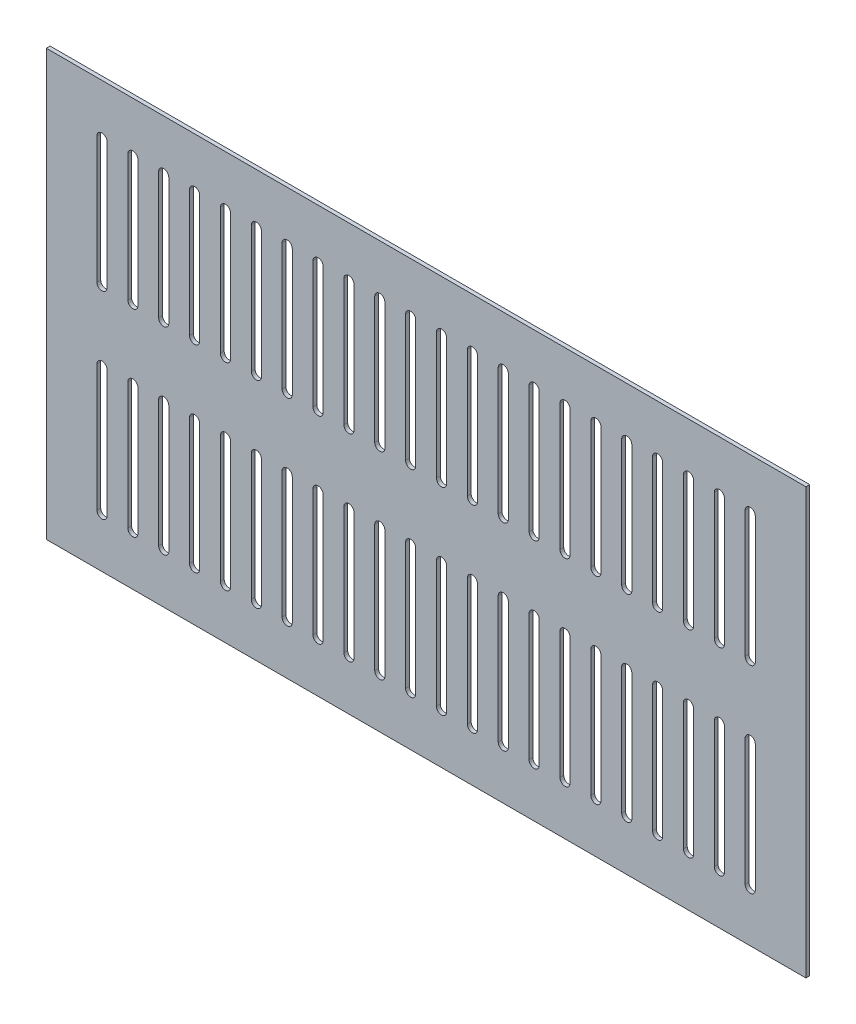
SolidWorks part; units mm, degrees
ref_plane "Ön Düzlem" through (0, 0, 0) normal (0, 0, 1) x (1, 0, 0)
ref_plane "Üst Düzlem" through (0, 0, 0) normal (0, 1, 0) x (1, 0, 0)
ref_plane "Sağ Düzlem" through (0, 0, 0) normal (1, 0, 0) x (0, 0, -1)
sketch "Çizim1" plane through (0, 0, 0) normal (0, 0, 1) x (1, 0, 0)
  line L0 (44, -40) -> (44, -140) construction
  line L1 (0, 0) -> (600, 0)
  line L2 (0, 0) -> (0, -336)
  line L3 (0, -336) -> (600, -336)
  line L4 (600, 0) -> (600, -336)
  line L5 (48, -40) -> (48, -140)
  line L6 (40, -40) -> (40, -140)
  line L7 (64.381, -40) -> (64.381, -140)
  line L8 (72.381, -40) -> (72.381, -140)
  line L9 (68.381, -40) -> (68.381, -140) construction
  line L10 (88.7619, -40) -> (88.7619, -140)
  line L11 (96.7619, -40) -> (96.7619, -140)
  line L12 (92.7619, -40) -> (92.7619, -140) construction
  line L13 (113.1429, -40) -> (113.1429, -140)
  line L14 (121.1429, -40) -> (121.1429, -140)
  line L15 (117.1429, -40) -> (117.1429, -140) construction
  line L16 (137.5238, -40) -> (137.5238, -140)
  line L17 (145.5238, -40) -> (145.5238, -140)
  line L18 (141.5238, -40) -> (141.5238, -140) construction
  line L19 (161.9048, -40) -> (161.9048, -140)
  line L20 (169.9048, -40) -> (169.9048, -140)
  line L21 (165.9048, -40) -> (165.9048, -140) construction
  line L22 (186.2857, -40) -> (186.2857, -140)
  line L23 (194.2857, -40) -> (194.2857, -140)
  line L24 (190.2857, -40) -> (190.2857, -140) construction
  line L25 (210.6667, -40) -> (210.6667, -140)
  line L26 (218.6667, -40) -> (218.6667, -140)
  line L27 (214.6667, -40) -> (214.6667, -140) construction
  line L28 (235.0476, -40) -> (235.0476, -140)
  line L29 (243.0476, -40) -> (243.0476, -140)
  line L30 (239.0476, -40) -> (239.0476, -140) construction
  line L31 (259.4286, -40) -> (259.4286, -140)
  line L32 (267.4286, -40) -> (267.4286, -140)
  line L33 (263.4286, -40) -> (263.4286, -140) construction
  line L34 (283.8095, -40) -> (283.8095, -140)
  line L35 (291.8095, -40) -> (291.8095, -140)
  line L36 (287.8095, -40) -> (287.8095, -140) construction
  line L37 (308.1905, -40) -> (308.1905, -140)
  line L38 (316.1905, -40) -> (316.1905, -140)
  line L39 (312.1905, -40) -> (312.1905, -140) construction
  line L40 (332.5714, -40) -> (332.5714, -140)
  line L41 (340.5714, -40) -> (340.5714, -140)
  line L42 (336.5714, -40) -> (336.5714, -140) construction
  line L43 (356.9524, -40) -> (356.9524, -140)
  line L44 (364.9524, -40) -> (364.9524, -140)
  line L45 (360.9524, -40) -> (360.9524, -140) construction
  line L46 (381.3333, -40) -> (381.3333, -140)
  line L47 (389.3333, -40) -> (389.3333, -140)
  line L48 (385.3333, -40) -> (385.3333, -140) construction
  line L49 (405.7143, -40) -> (405.7143, -140)
  line L50 (413.7143, -40) -> (413.7143, -140)
  line L51 (409.7143, -40) -> (409.7143, -140) construction
  line L52 (430.0952, -40) -> (430.0952, -140)
  line L53 (438.0952, -40) -> (438.0952, -140)
  line L54 (434.0952, -40) -> (434.0952, -140) construction
  line L55 (454.4762, -40) -> (454.4762, -140)
  line L56 (462.4762, -40) -> (462.4762, -140)
  line L57 (458.4762, -40) -> (458.4762, -140) construction
  line L58 (478.8571, -40) -> (478.8571, -140)
  line L59 (486.8571, -40) -> (486.8571, -140)
  line L60 (482.8571, -40) -> (482.8571, -140) construction
  line L61 (503.2381, -40) -> (503.2381, -140)
  line L62 (511.2381, -40) -> (511.2381, -140)
  line L63 (507.2381, -40) -> (507.2381, -140) construction
  line L64 (527.619, -40) -> (527.619, -140)
  line L65 (535.619, -40) -> (535.619, -140)
  line L66 (531.619, -40) -> (531.619, -140) construction
  line L67 (552, -40) -> (552, -140)
  line L68 (560, -40) -> (560, -140)
  line L69 (556, -40) -> (556, -140) construction
  line L70 (64.381, -196) -> (64.381, -296)
  line L71 (72.381, -196) -> (72.381, -296)
  line L72 (68.381, -196) -> (68.381, -296) construction
  line L73 (88.7619, -196) -> (88.7619, -296)
  line L74 (96.7619, -196) -> (96.7619, -296)
  line L75 (92.7619, -196) -> (92.7619, -296) construction
  line L76 (113.1429, -196) -> (113.1429, -296)
  line L77 (121.1429, -196) -> (121.1429, -296)
  line L78 (117.1429, -196) -> (117.1429, -296) construction
  line L79 (137.5238, -196) -> (137.5238, -296)
  line L80 (145.5238, -196) -> (145.5238, -296)
  line L81 (141.5238, -196) -> (141.5238, -296) construction
  line L82 (161.9048, -196) -> (161.9048, -296)
  line L83 (169.9048, -196) -> (169.9048, -296)
  line L84 (165.9048, -196) -> (165.9048, -296) construction
  line L85 (186.2857, -196) -> (186.2857, -296)
  line L86 (194.2857, -196) -> (194.2857, -296)
  line L87 (190.2857, -196) -> (190.2857, -296) construction
  line L88 (210.6667, -196) -> (210.6667, -296)
  line L89 (218.6667, -196) -> (218.6667, -296)
  line L90 (214.6667, -196) -> (214.6667, -296) construction
  line L91 (235.0476, -196) -> (235.0476, -296)
  line L92 (243.0476, -196) -> (243.0476, -296)
  line L93 (239.0476, -196) -> (239.0476, -296) construction
  line L94 (259.4286, -196) -> (259.4286, -296)
  line L95 (267.4286, -196) -> (267.4286, -296)
  line L96 (263.4286, -196) -> (263.4286, -296) construction
  line L97 (283.8095, -196) -> (283.8095, -296)
  line L98 (291.8095, -196) -> (291.8095, -296)
  line L99 (287.8095, -196) -> (287.8095, -296) construction
  line L100 (308.1905, -196) -> (308.1905, -296)
  line L101 (316.1905, -196) -> (316.1905, -296)
  line L102 (312.1905, -196) -> (312.1905, -296) construction
  line L103 (332.5714, -196) -> (332.5714, -296)
  line L104 (340.5714, -196) -> (340.5714, -296)
  line L105 (336.5714, -196) -> (336.5714, -296) construction
  line L106 (356.9524, -196) -> (356.9524, -296)
  line L107 (364.9524, -196) -> (364.9524, -296)
  line L108 (360.9524, -196) -> (360.9524, -296) construction
  line L109 (381.3333, -196) -> (381.3333, -296)
  line L110 (389.3333, -196) -> (389.3333, -296)
  line L111 (385.3333, -196) -> (385.3333, -296) construction
  line L112 (405.7143, -196) -> (405.7143, -296)
  line L113 (413.7143, -196) -> (413.7143, -296)
  line L114 (409.7143, -196) -> (409.7143, -296) construction
  line L115 (430.0952, -196) -> (430.0952, -296)
  line L116 (438.0952, -196) -> (438.0952, -296)
  line L117 (434.0952, -196) -> (434.0952, -296) construction
  line L118 (454.4762, -196) -> (454.4762, -296)
  line L119 (462.4762, -196) -> (462.4762, -296)
  line L120 (458.4762, -196) -> (458.4762, -296) construction
  line L121 (478.8571, -196) -> (478.8571, -296)
  line L122 (486.8571, -196) -> (486.8571, -296)
  line L123 (482.8571, -196) -> (482.8571, -296) construction
  line L124 (503.2381, -196) -> (503.2381, -296)
  line L125 (511.2381, -196) -> (511.2381, -296)
  line L126 (507.2381, -196) -> (507.2381, -296) construction
  line L127 (527.619, -196) -> (527.619, -296)
  line L128 (535.619, -196) -> (535.619, -296)
  line L129 (531.619, -196) -> (531.619, -296) construction
  line L130 (552, -196) -> (552, -296)
  line L131 (560, -196) -> (560, -296)
  line L132 (556, -196) -> (556, -296) construction
  line L133 (40, -196) -> (40, -296)
  line L134 (48, -196) -> (48, -296)
  line L135 (44, -196) -> (44, -296) construction
  arc A0 (48, -40) -> (40, -40) centre (44, -40) ccw
  arc A1 (40, -140) -> (48, -140) centre (44, -140) ccw
  arc A2 (72.381, -40) -> (64.381, -40) centre (68.381, -40) ccw
  arc A3 (64.381, -140) -> (72.381, -140) centre (68.381, -140) ccw
  arc A4 (96.7619, -40) -> (88.7619, -40) centre (92.7619, -40) ccw
  arc A5 (88.7619, -140) -> (96.7619, -140) centre (92.7619, -140) ccw
  arc A6 (121.1429, -40) -> (113.1429, -40) centre (117.1429, -40) ccw
  arc A7 (113.1429, -140) -> (121.1429, -140) centre (117.1429, -140) ccw
  arc A8 (145.5238, -40) -> (137.5238, -40) centre (141.5238, -40) ccw
  arc A9 (137.5238, -140) -> (145.5238, -140) centre (141.5238, -140) ccw
  arc A10 (169.9048, -40) -> (161.9048, -40) centre (165.9048, -40) ccw
  arc A11 (161.9048, -140) -> (169.9048, -140) centre (165.9048, -140) ccw
  arc A12 (194.2857, -40) -> (186.2857, -40) centre (190.2857, -40) ccw
  arc A13 (186.2857, -140) -> (194.2857, -140) centre (190.2857, -140) ccw
  arc A14 (218.6667, -40) -> (210.6667, -40) centre (214.6667, -40) ccw
  arc A15 (210.6667, -140) -> (218.6667, -140) centre (214.6667, -140) ccw
  arc A16 (243.0476, -40) -> (235.0476, -40) centre (239.0476, -40) ccw
  arc A17 (235.0476, -140) -> (243.0476, -140) centre (239.0476, -140) ccw
  arc A18 (267.4286, -40) -> (259.4286, -40) centre (263.4286, -40) ccw
  arc A19 (259.4286, -140) -> (267.4286, -140) centre (263.4286, -140) ccw
  arc A20 (291.8095, -40) -> (283.8095, -40) centre (287.8095, -40) ccw
  arc A21 (283.8095, -140) -> (291.8095, -140) centre (287.8095, -140) ccw
  arc A22 (316.1905, -40) -> (308.1905, -40) centre (312.1905, -40) ccw
  arc A23 (308.1905, -140) -> (316.1905, -140) centre (312.1905, -140) ccw
  arc A24 (340.5714, -40) -> (332.5714, -40) centre (336.5714, -40) ccw
  arc A25 (332.5714, -140) -> (340.5714, -140) centre (336.5714, -140) ccw
  arc A26 (364.9524, -40) -> (356.9524, -40) centre (360.9524, -40) ccw
  arc A27 (356.9524, -140) -> (364.9524, -140) centre (360.9524, -140) ccw
  arc A28 (389.3333, -40) -> (381.3333, -40) centre (385.3333, -40) ccw
  arc A29 (381.3333, -140) -> (389.3333, -140) centre (385.3333, -140) ccw
  arc A30 (413.7143, -40) -> (405.7143, -40) centre (409.7143, -40) ccw
  arc A31 (405.7143, -140) -> (413.7143, -140) centre (409.7143, -140) ccw
  arc A32 (438.0952, -40) -> (430.0952, -40) centre (434.0952, -40) ccw
  arc A33 (430.0952, -140) -> (438.0952, -140) centre (434.0952, -140) ccw
  arc A34 (462.4762, -40) -> (454.4762, -40) centre (458.4762, -40) ccw
  arc A35 (454.4762, -140) -> (462.4762, -140) centre (458.4762, -140) ccw
  arc A36 (486.8571, -40) -> (478.8571, -40) centre (482.8571, -40) ccw
  arc A37 (478.8571, -140) -> (486.8571, -140) centre (482.8571, -140) ccw
  arc A38 (511.2381, -40) -> (503.2381, -40) centre (507.2381, -40) ccw
  arc A39 (503.2381, -140) -> (511.2381, -140) centre (507.2381, -140) ccw
  arc A40 (535.619, -40) -> (527.619, -40) centre (531.619, -40) ccw
  arc A41 (527.619, -140) -> (535.619, -140) centre (531.619, -140) ccw
  arc A42 (560, -40) -> (552, -40) centre (556, -40) ccw
  arc A43 (552, -140) -> (560, -140) centre (556, -140) ccw
  arc A44 (72.381, -196) -> (64.381, -196) centre (68.381, -196) ccw
  arc A45 (64.381, -296) -> (72.381, -296) centre (68.381, -296) ccw
  arc A46 (96.7619, -196) -> (88.7619, -196) centre (92.7619, -196) ccw
  arc A47 (88.7619, -296) -> (96.7619, -296) centre (92.7619, -296) ccw
  arc A48 (121.1429, -196) -> (113.1429, -196) centre (117.1429, -196) ccw
  arc A49 (113.1429, -296) -> (121.1429, -296) centre (117.1429, -296) ccw
  arc A50 (145.5238, -196) -> (137.5238, -196) centre (141.5238, -196) ccw
  arc A51 (137.5238, -296) -> (145.5238, -296) centre (141.5238, -296) ccw
  arc A52 (169.9048, -196) -> (161.9048, -196) centre (165.9048, -196) ccw
  arc A53 (161.9048, -296) -> (169.9048, -296) centre (165.9048, -296) ccw
  arc A54 (194.2857, -196) -> (186.2857, -196) centre (190.2857, -196) ccw
  arc A55 (186.2857, -296) -> (194.2857, -296) centre (190.2857, -296) ccw
  arc A56 (218.6667, -196) -> (210.6667, -196) centre (214.6667, -196) ccw
  arc A57 (210.6667, -296) -> (218.6667, -296) centre (214.6667, -296) ccw
  arc A58 (243.0476, -196) -> (235.0476, -196) centre (239.0476, -196) ccw
  arc A59 (235.0476, -296) -> (243.0476, -296) centre (239.0476, -296) ccw
  arc A60 (267.4286, -196) -> (259.4286, -196) centre (263.4286, -196) ccw
  arc A61 (259.4286, -296) -> (267.4286, -296) centre (263.4286, -296) ccw
  arc A62 (291.8095, -196) -> (283.8095, -196) centre (287.8095, -196) ccw
  arc A63 (283.8095, -296) -> (291.8095, -296) centre (287.8095, -296) ccw
  arc A64 (316.1905, -196) -> (308.1905, -196) centre (312.1905, -196) ccw
  arc A65 (308.1905, -296) -> (316.1905, -296) centre (312.1905, -296) ccw
  arc A66 (340.5714, -196) -> (332.5714, -196) centre (336.5714, -196) ccw
  arc A67 (332.5714, -296) -> (340.5714, -296) centre (336.5714, -296) ccw
  arc A68 (364.9524, -196) -> (356.9524, -196) centre (360.9524, -196) ccw
  arc A69 (356.9524, -296) -> (364.9524, -296) centre (360.9524, -296) ccw
  arc A70 (389.3333, -196) -> (381.3333, -196) centre (385.3333, -196) ccw
  arc A71 (381.3333, -296) -> (389.3333, -296) centre (385.3333, -296) ccw
  arc A72 (413.7143, -196) -> (405.7143, -196) centre (409.7143, -196) ccw
  arc A73 (405.7143, -296) -> (413.7143, -296) centre (409.7143, -296) ccw
  arc A74 (438.0952, -196) -> (430.0952, -196) centre (434.0952, -196) ccw
  arc A75 (430.0952, -296) -> (438.0952, -296) centre (434.0952, -296) ccw
  arc A76 (462.4762, -196) -> (454.4762, -196) centre (458.4762, -196) ccw
  arc A77 (454.4762, -296) -> (462.4762, -296) centre (458.4762, -296) ccw
  arc A78 (486.8571, -196) -> (478.8571, -196) centre (482.8571, -196) ccw
  arc A79 (478.8571, -296) -> (486.8571, -296) centre (482.8571, -296) ccw
  arc A80 (511.2381, -196) -> (503.2381, -196) centre (507.2381, -196) ccw
  arc A81 (503.2381, -296) -> (511.2381, -296) centre (507.2381, -296) ccw
  arc A82 (535.619, -196) -> (527.619, -196) centre (531.619, -196) ccw
  arc A83 (527.619, -296) -> (535.619, -296) centre (531.619, -296) ccw
  arc A84 (560, -196) -> (552, -196) centre (556, -196) ccw
  arc A85 (552, -296) -> (560, -296) centre (556, -296) ccw
  arc A86 (48, -196) -> (40, -196) centre (44, -196) ccw
  arc A87 (40, -296) -> (48, -296) centre (44, -296) ccw
  point P7 (44, -90)
  point P16 (68.381, -90)
  point P23 (92.7619, -90)
  point P30 (117.1429, -90)
  point P37 (141.5238, -90)
  point P44 (165.9048, -90)
  point P51 (190.2857, -90)
  point P58 (214.6667, -90)
  point P65 (239.0476, -90)
  point P72 (263.4286, -90)
  point P79 (287.8095, -90)
  point P86 (312.1905, -90)
  point P93 (336.5714, -90)
  point P100 (360.9524, -90)
  point P107 (385.3333, -90)
  point P114 (409.7143, -90)
  point P121 (434.0952, -90)
  point P128 (458.4762, -90)
  point P135 (482.8571, -90)
  point P142 (507.2381, -90)
  point P149 (531.619, -90)
  point P156 (556, -90)
  point P163 (68.381, -246)
  point P170 (92.7619, -246)
  point P177 (117.1429, -246)
  point P184 (141.5238, -246)
  point P191 (165.9048, -246)
  point P198 (190.2857, -246)
  point P205 (214.6667, -246)
  point P212 (239.0476, -246)
  point P219 (263.4286, -246)
  point P226 (287.8095, -246)
  point P233 (312.1905, -246)
  point P240 (336.5714, -246)
  point P247 (360.9524, -246)
  point P254 (385.3333, -246)
  point P261 (409.7143, -246)
  point P268 (434.0952, -246)
  point P275 (458.4762, -246)
  point P282 (482.8571, -246)
  point P289 (507.2381, -246)
  point P296 (531.619, -246)
  point P303 (556, -246)
  point P310 (44, -246)
  dimension "D5" = 40
  dimension "D10" = 56
  dimension "D1" = 600
  dimension "D2" = 336
  dimension "D3" = 8
  dimension "D4" = 100
  dimension "D6" = 40
  dimension "D9" = 40
  dimension "D11" = 40
  dimension "D7" = 22
  dimension "D8" = 2
extrude "Yükseklik-Ekstrüzyon1" add sketch "Çizim1" along normal blind 3
